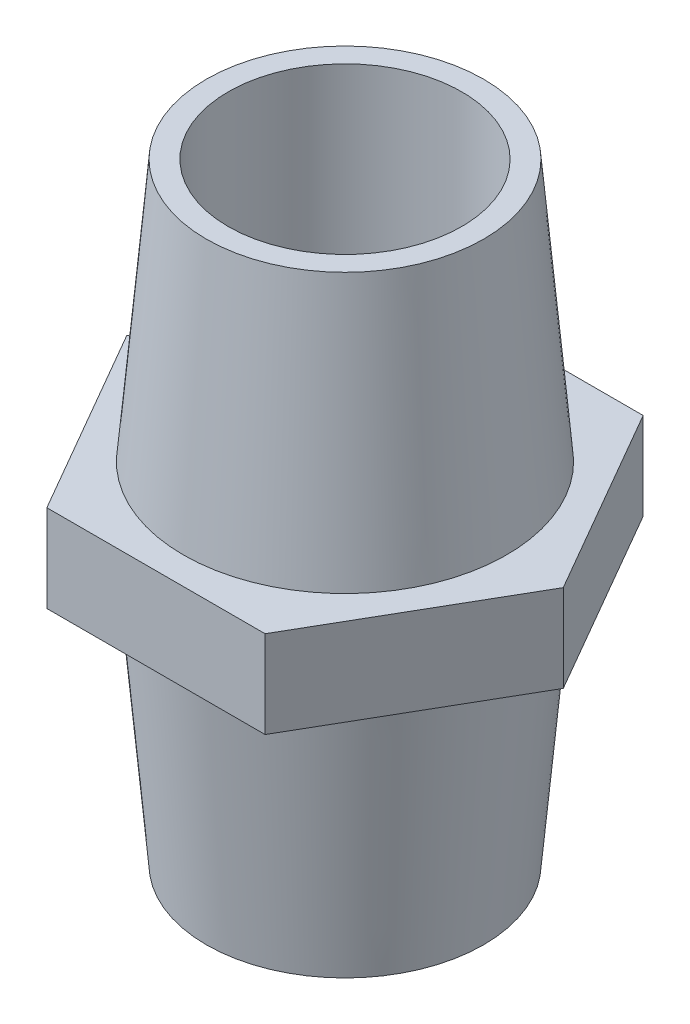
SolidWorks part; units mm, degrees
ref_plane "Alzado" through (0, 0, 0) normal (0, 0, 1) x (1, 0, 0)
ref_plane "Planta" through (0, 0, 0) normal (0, 1, 0) x (1, 0, 0)
ref_plane "Vista lateral" through (0, 0, 0) normal (1, 0, 0) x (0, 0, -1)
sketch "Croquis1" plane through (0, 0, 0) normal (0, 0, 1) x (1, 0, 0)
  line L0 (0, 30.3344) -> (0, -23.6449) construction
  line L1 (8.025, 24) -> (8.025, -18)
  line L2 (8.025, -18) -> (9.525, -18)
  line L3 (9.525, -18) -> (11.11, 0)
  line L4 (11.11, 0) -> (15, 0)
  line L5 (15, 0) -> (15, 6)
  line L6 (15, 6) -> (11.11, 6)
  line L7 (11.11, 6) -> (9.525, 24)
  line L8 (9.525, 24) -> (8.025, 24)
  dimension "D1" = 18
  dimension "D2" = 18
  dimension "D3" = 42
  dimension "D4" = 15
  dimension "D5" = 9.525
  dimension "D6" = 1.5
  dimension "D7" = 1.5
  dimension "D8" = 11.11
revolve "Revolución1" add sketch "Croquis1" angle 360 about L0
sketch "Croquis2" plane through (0, 6, 0) normal (0, 1, 0) x (1, 0, 0)
  line L1 (15, 0) -> (7.5, 12.9904)
  line L2 (7.5, 12.9904) -> (-7.5, 12.9904)
  line L3 (-7.5, 12.9904) -> (-15, 0)
  line L4 (-15, 0) -> (-7.5, -12.9904)
  line L5 (-7.5, -12.9904) -> (7.5, -12.9904)
  line L6 (7.5, -12.9904) -> (15, 0)
  circle A0 centre (0, 0) radius 12.9904 construction
extrude "Cortar-Extruir1" cut sketch "Croquis2" against normal through all flip side to cut
sketch "Croquis3" plane through (0, 0, 0) normal (0, -1, 0) x (1, 0, 0)
  circle A0 centre (0, 0) radius 11.11
  circle A1 centre (0, 0) radius 11.11
